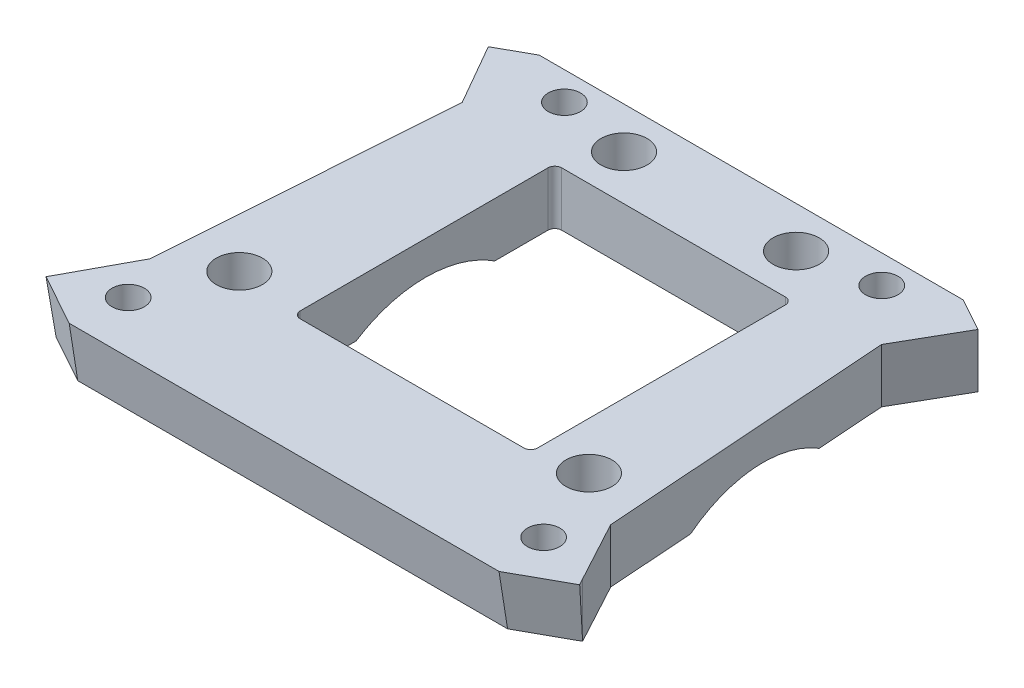
SolidWorks part; units mm, degrees
ref_plane "Front Plane" through (0, 0, 0) normal (0, 0, 1) x (1, 0, 0)
ref_plane "Top Plane" through (0, 0, 0) normal (0, 1, 0) x (1, 0, 0)
ref_plane "Right Plane" through (0, 0, 0) normal (1, 0, 0) x (0, 0, -1)
sketch "Sketch1" plane through (0, 0, 0) normal (0, 1, 0) x (1, 0, 0)
  line L0 (0, 32.5988) -> (0, -35.2934) construction
  line L1 (-31.8681, 0) -> (31.8681, 0) construction
  line L2 (28.5569, 32.5988) -> (-28.5569, 32.5988)
  line L5 (-35.5769, 28.7142) -> (-30.4673, 19.813)
  line L7 (-28.5569, 32.5988) -> (-35.5769, 28.7142)
  line L8 (-30.4673, 19.813) -> (-33.462, -22.5447)
  line L9 (-33.462, -22.5447) -> (-38.2469, -31.4089)
  line L10 (38.2469, -31.4089) -> (31.2269, -35.2934)
  line L13 (-38.2469, -31.4089) -> (-31.2269, -35.2934)
  line L29 (33.462, -22.5447) -> (38.2469, -31.4089)
  line L30 (30.4673, 19.813) -> (33.462, -22.5447)
  line L31 (35.5769, 28.7142) -> (30.4673, 19.813)
  line L32 (28.5569, 32.5988) -> (35.5769, 28.7142)
  line L33 (-31.2269, -35.2934) -> (31.2269, -35.2934)
  dimension "D1" = 28.5569
  dimension "D2" = 151.042
  dimension "D3" = 32.5988
  dimension "D4" = 204.316
  dimension "D5" = 62.4538
  dimension "D6" = 8.0231
  dimension "D7" = 151.042
  dimension "D8" = 10.2634
  dimension "D9" = 42.4635
  dimension "D10" = 94.044
  dimension "D11" = 10.0731
  dimension "D12" = 89.101
  dimension "D13" = 90.598
  dimension "D15" = 8.0231
extrude "Boss-Extrude1" add sketch "Sketch1" along normal blind 10
sketch "Sketch3" plane through (0, 0, 0) normal (1, 0, 0) x (0, 0, -1)
  line L0 (32.5988, 0) -> (-35.2934, 0)
  line L1 (32.5988, 0) -> (31.3544, 7.8529)
  line L3 (32.5988, 0) -> (35.5458, 0) construction
  line L7 (-35.2934, 10) -> (-35.2934, 0) construction
  line L8 (-35.2934, 12.6812) -> (31.4343, 12.6812)
  line L9 (31.4343, 12.6812) -> (34.0723, 12.6812)
  line L10 (34.0723, 12.6812) -> (34.0723, 0)
  line L11 (34.0723, 0) -> (32.5988, 0)
  line L12 (31.3544, 7.8529) -> (-36.5378, 7.8529)
  line L14 (-36.5378, 7.8529) -> (-35.2934, 0)
  line L15 (-35.2934, 10) -> (-35.2934, 0)
  line L16 (-35.2934, 10) -> (-35.2934, 12.6812)
  dimension "D1" = 7.9509
  dimension "D2" = 7.9509
  dimension "D3" = 99.004
  dimension "D4" = 99.004
  dimension "D5" = 67.8922
  dimension "D6" = 2.638
  dimension "D7" = 12.6812
  dimension "D8" = 1.4735
extrude "Cut-Extrude1" cut sketch "Sketch3" against normal through all and the other way through all contours L16 L15 L12 L1 L11 L10 L9 L8
sketch "Sketch5" plane through (0, 0, 0) normal (1, 0, 0) x (0, 0, -1)
  line L0 (-35.2934, 10) -> (-35.2934, 0) construction
  line L1 (31.3544, 7.8529) -> (-36.5378, 7.8529) construction
  line L2 (-36.5378, 7.8529) -> (-35.2934, 0) construction
  line L3 (-35.2934, 10) -> (-35.2934, 0)
  line L4 (31.3544, 7.8529) -> (-36.5378, 7.8529)
  line L5 (-36.5378, 7.8529) -> (-35.2934, 0)
extrude "Boss-Extrude2" add sketch "Sketch5" along normal up to vertex (31.2269 mm away) and the other way up to vertex (31.2269 mm away) contours L4 L5 L3
sketch "Sketch7" plane through (0, 7.8529, 0) normal (0, 1, 0) x (1, 0, 0)
  line L0 (31.2269, -35.2934) -> (38.2469, -31.4089) construction
  line L1 (31.2269, -35.2934) -> (31.2269, -36.5378) construction
  line L2 (31.2269, -35.2934) -> (38.2469, -31.4089)
  line L3 (31.2269, -35.2934) -> (31.2269, -36.5378)
  line L4 (31.2269, -36.5378) -> (38.774, -32.3615)
  line L5 (38.2469, -31.4089) -> (38.774, -32.3615)
extrude "Boss-Extrude4" add sketch "Sketch7" against normal up to vertex (7.8529 mm away)
sketch3d "3DSketch2"
  line L0 (31.2269, 7.8529, 36.5378) -> (31.2269, 0, 35.2934) construction
sketch "Sketch12" plane through (0, 0, 0) normal (0, 0.9877, 0.1565) x (1, 0, 0)
  line L0 (31.2269, -36.0875) -> (38.774, -31.9627) construction
  line L1 (-31.2269, -34.8585) -> (31.2269, -34.8585) construction
  line L2 (31.2269, -36.0875) -> (38.774, -31.9627)
  line L3 (-31.2269, -34.8585) -> (31.2269, -34.8585)
  line L4 (30.8962, -34.8585) -> (30.8962, -36.2682)
  line L5 (30.8962, -36.2682) -> (31.2269, -36.0875)
  line L6 (38.774, -31.9627) -> (39.4579, -31.589)
  line L7 (31.2269, -34.8585) -> (38.9407, -30.6426)
  line L8 (39.4579, -31.589) -> (38.9407, -30.6426)
  dimension "D1" = 0.7794
  dimension "D2" = 0.3307
extrude "Cut-Extrude6" cut sketch "Sketch12" along normal up to surface (13.4744 mm away) contours L6 L8 L7 L3 L4 L5 L2
sketch "Sketch13" plane through (0, 7.8529, 0) normal (0, 1, 0) x (1, 0, 0)
  line L0 (-31.2269, -35.2934) -> (-31.2269, -36.5378) construction
  line L1 (-38.2469, -31.4089) -> (-31.2269, -35.2934) construction
  line L2 (-31.2269, -35.2934) -> (-31.2269, -36.5378)
  line L3 (-38.2469, -31.4089) -> (-31.2269, -35.2934)
  line L4 (-31.2269, -36.5378) -> (-38.774, -32.3615)
  line L5 (-38.774, -32.3615) -> (-38.2469, -31.4089)
extrude "Boss-Extrude6" add sketch "Sketch13" against normal up to vertex (7.8529 mm away)
sketch "Sketch14" plane through (0, 0, 0) normal (0, 0.9877, 0.1565) x (1, 0, 0)
  line L0 (-31.2269, -34.8585) -> (31.2269, -34.8585) construction
  line L1 (-38.774, -31.9627) -> (-31.2269, -36.0875) construction
  line L2 (-31.2269, -34.8585) -> (31.2269, -34.8585)
  line L3 (-38.774, -31.9627) -> (-31.2269, -36.0875)
  line L4 (-31.2269, -34.8585) -> (-39.1386, -30.5345)
  line L5 (-39.1386, -30.5345) -> (-40.9861, -30.7538)
  line L6 (-40.9861, -30.7538) -> (-38.774, -31.9627)
  line L7 (-31.2269, -36.0875) -> (-31.2269, -34.8585)
  dimension "D1" = 1.8475
  dimension "D2" = 9.0162
extrude "Cut-Extrude7" cut sketch "Sketch14" along normal up to surface (12.7893 mm away) contours L3 L7 L4 L5 L6
sketch "Sketch15" plane through (0, 7.8529, 0) normal (0, 1, 0) x (1, 0, 0)
  line L0 (0, -19.1987) -> (0, 18.8013) construction
  line L1 (-16, -0.1987) -> (18.5, -0.1987) construction
  line L3 (-16, 18.8013) -> (18.5, 18.8013)
  line L4 (18.5, 18.8013) -> (18.5, -19.1987)
  line L5 (18.5, -19.1987) -> (-16, -19.1987)
  line L7 (-16, -19.1987) -> (-16, 18.8013)
  point P10 (-16, -0.1987)
  dimension "D1" = 38
  dimension "D2" = 16
  dimension "D3" = 18.5
  dimension "D4" = 0.1987
extrude "Cut-Extrude8" cut sketch "Sketch15" against normal through all
fillet "Fillet1" radius 1 4 edges at (18.5, 3.9265, 19.1987) (18.5, 3.9265, -18.8013) (-16, 3.9265, -18.8013) (-16, 3.9265, 19.1987)
sketch "Sketch16" plane through (0, 7.8529, 0) normal (0, 1, 0) x (1, 0, 0)
  circle A0 centre (30.184, -29.0132) radius 2.35 construction
  circle A1 centre (-30.184, -29.0132) radius 2.35 construction
  arc A2 (-23.165, 24.9012) -> (-23.1693, 24.9014) centre (-23.0569, 27.2488) ccw construction
  arc A3 (23.1693, 24.9014) -> (23.165, 24.9012) centre (23.0569, 27.2488) ccw construction
  circle A4 centre (30.184, -29.0132) radius 2.35
  circle A5 centre (-30.184, -29.0132) radius 2.35
  arc A6 (-23.165, 24.9012) -> (-23.1693, 24.9014) centre (-23.0569, 27.2488) ccw
  arc A7 (23.1693, 24.9014) -> (23.165, 24.9012) centre (23.0569, 27.2488) ccw
  circle A8 centre (-23.0569, 27.2488) radius 2.35
  circle A9 centre (23.0569, 27.2488) radius 2.35
extrude "Cut-Extrude9" cut sketch "Sketch16" against normal up to surface (7.8529 mm away) contours A6 A8 | A5 | A4 | A7 A9 up to face at (1.25, 0, 0.1987)
sketch "Sketch17" plane through (0, 7.8529, 0) normal (0, 1, 0) x (1, 0, 0)
  line L0 (0, 0) -> (0, 31.3544) construction
  line L1 (-30.8056, 31.3544) -> (30.8056, 31.3544) construction
sketch "Sketch18" plane through (0, 7.8529, 0) normal (0, 1, 0) x (1, 0, 0)
  circle A0 centre (-25.3976, -17.6468) radius 3.35 construction
  circle A1 centre (12.5003, 25.355) radius 3.35 construction
  circle A2 centre (-12.4997, 25.3538) radius 3.35 construction
  circle A3 centre (25.4024, -17.6443) radius 3.35 construction
  circle A4 centre (-25.3976, -17.6468) radius 3.35
  circle A5 centre (12.5003, 25.355) radius 3.35
  circle A6 centre (-12.4997, 25.3538) radius 3.35
  circle A7 centre (25.4024, -17.6443) radius 3.35
extrude "Cut-Extrude10" cut sketch "Sketch18" against normal up to surface (7.8529 mm away) up to face at (23.0569, 0, -24.8988)
sketch "Sketch19" plane through (-16, 0, 0) normal (1, 0, 0) x (0, 0, -1)
  line L0 (0, 0) -> (0, 4.1299) construction
  line L1 (17.8013, 0) -> (-18.1987, 0) construction
  line L2 (10.0651, 0) -> (-10.0633, 0)
  spline S5 degree 3 poles (0.0009, 2.9675) (-0.5427, 2.9675) (-1.6177, 2.9212) (-3.8522, 2.6256) (-6.6825, 1.8459) (-9.9668, 0.2082) (-12.9181, -2.0959) (-15.3469, -4.9456) (-17.1242, -8.1564) (-18.0248, -10.9507) (-18.4161, -13.1704) (-18.5086, -14.2424) (-18.5319, -14.7855) knots 0 0 0 0 0.0625 0.125 0.25 0.375 0.5 0.625 0.75 0.875 0.9375 1 1 1 1
  spline S6 degree 3 poles (0.0009, 2.9675) (0.5445, 2.9675) (1.6196, 2.9212) (3.854, 2.6256) (6.6844, 1.8459) (9.9686, 0.2082) (12.92, -2.0959) (15.3488, -4.9456) (17.1261, -8.1564) (18.0267, -10.9507) (18.418, -13.1704) (18.5105, -14.2424) (18.5338, -14.7855) knots 0 0 0 0 0.0625 0.125 0.25 0.375 0.5 0.625 0.75 0.875 0.9375 1 1 1 1
  line M1 (-18.1987, 0) -> (17.8013, 0)
extrude "Cut-Extrude11" cut sketch "Sketch19" against normal through all and the other way through all contours L0 S5 M1 | L0 L2 S6 S5
